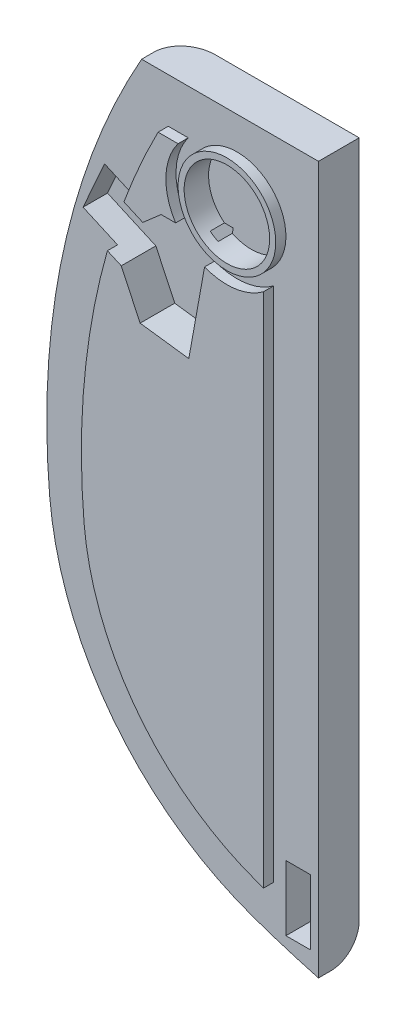
SolidWorks part; units mm, degrees
ref_plane "Front Plane" through (0, 0, 0) normal (0, 0, 1) x (1, 0, 0)
ref_plane "Top Plane" through (0, 0, 0) normal (0, 1, 0) x (1, 0, 0)
ref_plane "Right Plane" through (0, 0, 0) normal (1, 0, 0) x (0, 0, -1)
sketch "Sketch1" plane through (0, 0, 0) normal (0, 0, 1) x (1, 0, 0)
  line L0 (0, 0) -> (-43.45, 0)
  line L1 (98.6128, 0) -> (-98.6128, 0) construction
  line L2 (-43.45, 0) -> (112.55, -88.38) construction
  line L3 (-66.0453, -104.2148) -> (9.2593, -97.5381) construction
  line L4 (0, 0) -> (0, -173.7617)
  arc A0 (-43.45, 0) -> (-66.0453, -104.2148) centre (112.55, -88.38) ccw
  arc A1 (-66.0453, -104.2148) -> (-15.8934, -168.8311) centre (9.2593, -97.5381) ccw
  arc A2 (-15.8934, -168.8311) -> (0, -173.7617) centre (56.2868, 35.7571) ccw
  dimension "D1" = 43.45
  dimension "D2" = 156
  dimension "D3" = 88.38
extrude "Boss-Extrude1" add sketch "Sketch1" along normal blind 10 contours A0 A1 A2 L4 L0
fillet "Fillet1" radius 7 3 edges at (-62.6747, -50.3887, 0) (-7.994, -171.4489, 0) (-50.4629, -143.8913, 0)
sketch "Sketch7" plane through (0, 0, 10) normal (0, 0, 1) x (1, 0, 0)
  line L0 (-43.45, 0) -> (-57.5496, -31.6954) construction
  line L1 (-57.5496, -31.6954) -> (-49.2536, -35.3858) construction
  line L2 (-49.2536, -35.3858) -> (-55.1925, -32.7439) construction
  line L7 (-55.1925, -32.7439) -> (-52.4281, -26.5297) construction
  line L8 (-55.1925, -32.7439) -> (-52.5506, -26.805)
  line L9 (-52.5506, -26.805) -> (-40.6728, -32.0888)
  line L11 (-45.9566, -43.9666) -> (-57.8344, -38.6828)
  line L12 (-57.8344, -38.6828) -> (-55.1925, -32.7439)
  line L13 (-45.9566, -43.9666) -> (-41.3162, -53.8453)
  line L14 (-41.3162, -53.8453) -> (-29.358, -55.4136)
  line L15 (-29.358, -55.4136) -> (-24.4348, -28.1595)
  line L16 (-24.4348, -28.1595) -> (-36.1664, -28.1595)
  line L17 (-36.1664, -28.1595) -> (-40.6728, -32.0888)
  arc A0 (-43.45, 0) -> (-66.0453, -104.2148) centre (112.55, -88.38) ccw construction
  dimension "D1" = 34.69
  dimension "D2" = 6.5
  dimension "D3" = 13
  dimension "D4" = 13
extrude "Cut-Extrude5" cut sketch "Sketch7" against normal blind 6 contours L11 L12 L8 L9 L17 L16 L15 L14 L13
sketch "Sketch9" plane through (0, 0, 10) normal (0, 0, 1) x (1, 0, 0)
  line L0 (0, 0) -> (-20, 0) construction
  line L1 (-20, 0) -> (-20, -11) construction
  line L2 (-36.1664, -28.1595) -> (-40.6728, -32.0888) construction
  line L3 (-24.4348, -28.1595) -> (-36.1664, -28.1595) construction
  line L4 (-11, -11) -> (-36.9018, -11)
  line L5 (-11, -158.8887) -> (-11, -11)
  line L7 (-11, -158.8887) -> (-11, -32)
  line L8 (-29.358, -55.4136) -> (-24.4348, -28.1595) construction
  line L9 (-41.3162, -53.8453) -> (-29.358, -55.4136) construction
  line L10 (-45.9566, -43.9666) -> (-41.3162, -53.8453) construction
  line L11 (-45.9566, -43.9666) -> (-57.8344, -38.6828) construction
  line L12 (-32, -11) -> (-36.9018, -11)
  line L13 (-52.5506, -26.805) -> (-40.6728, -32.0888) construction
  line L14 (-36.1664, -28.1595) -> (-40.6728, -32.0888)
  line L15 (-32.5866, -28.1595) -> (-36.1664, -28.1595)
  line L16 (-29.358, -55.4136) -> (-25.483, -33.962)
  line L17 (-41.3162, -53.8453) -> (-29.358, -55.4136)
  line L18 (-45.9566, -43.9666) -> (-41.3162, -53.8453)
  line L19 (-45.9566, -43.9666) -> (-49.3582, -42.4534)
  line L21 (-45.306, -30.0278) -> (-40.6728, -32.0888)
  arc A0 (-25.483, -33.962) -> (-11, -32) centre (-20, -20) ccw
  arc A1 (-32, -11) -> (-32.5866, -28.1595) centre (-20, -20) ccw
  arc A3 (-49.3582, -42.4534) -> (-55.0883, -103.2433) centre (112.55, -88.38) ccw
  arc A6 (-36.9018, -11) -> (-55.0883, -103.2433) centre (112.55, -88.38) ccw
  arc A7 (-55.0883, -103.2433) -> (-12.2337, -158.4578) centre (9.2593, -97.5381) ccw
  arc A8 (-12.2337, -158.4578) -> (-11, -158.8887) centre (56.2868, 35.7571) ccw
  arc A9 (-36.9018, -11) -> (-45.306, -30.0278) centre (112.55, -88.38) ccw
  arc A10 (-55.0883, -103.2433) -> (-12.2337, -158.4578) centre (9.2593, -97.5381) ccw
  arc A11 (-12.2337, -158.4578) -> (-11, -158.8887) centre (56.2868, 35.7571) ccw
  dimension "D1" = 11
extrude "Boss-Extrude2" add sketch "Sketch9" along normal blind 2.5
sketch "Sketch10" plane through (0, 0, 10) normal (0, 0, 1) x (1, 0, 0)
  line L0 (-17.9864, -34.8642) -> (-20, -20) construction
  arc A0 (-25.483, -33.962) -> (-11, -32) centre (-20, -20) ccw construction
  circle A1 centre (-20, -20) radius 12
extrude "Boss-Extrude3" add sketch "Sketch10" along normal blind 2.5
sketch "Sketch11" plane through (0, 0, 12.5) normal (0, 0, 1) x (1, 0, 0)
  line L0 (-16.9335, -31.6016) -> (-20, -20) construction
  circle A0 centre (-20, -20) radius 12 construction
  circle A1 centre (-20, -20) radius 10.5
extrude "Cut-Extrude6" cut sketch "Sketch11" against normal blind 6
sketch "Sketch12" plane through (0, 0, 10) normal (0, 0, 1) x (1, 0, 0)
  line L0 (0, -173.7617) -> (0, -168.7617) construction
  line L1 (0, -168.7617) -> (-2, -168.7617) construction
  line L2 (-2, -168.7617) -> (-8, -168.7617)
  line L3 (-8, -168.7617) -> (-8, -152.7617)
  line L4 (-8, -152.7617) -> (-2, -152.7617)
  line L5 (-2, -152.7617) -> (-2, -168.7617)
  arc A0 (-15.8934, -168.8311) -> (0, -173.7617) centre (56.2868, 35.7571) ccw construction
  dimension "D1" = 2
  dimension "D2" = 6
extrude "Cut-Extrude7" cut sketch "Sketch12" against normal blind 6
